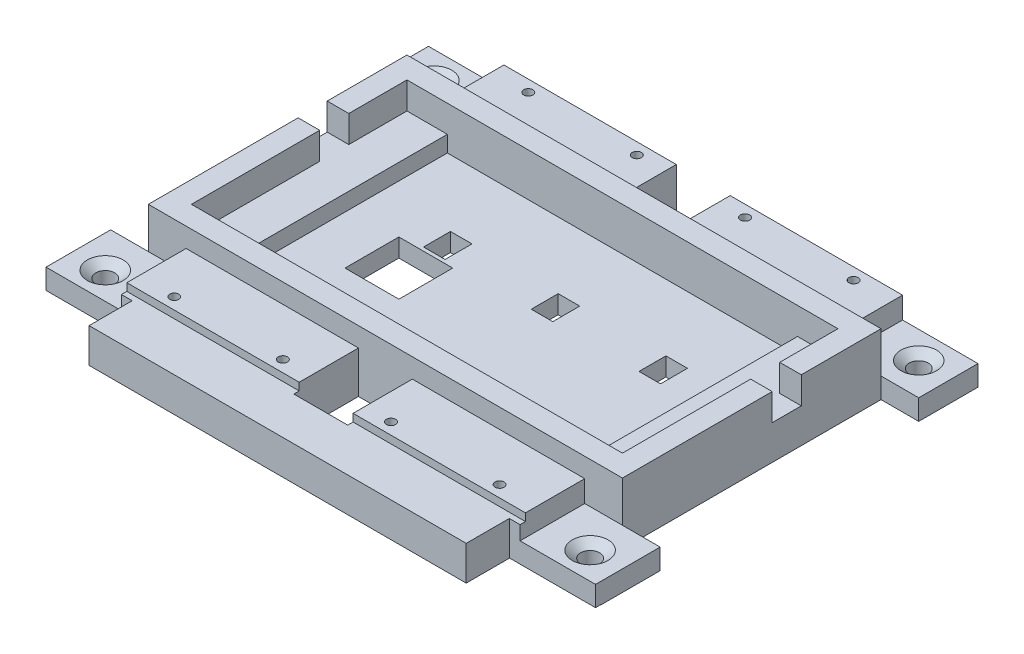
SolidWorks part; units mm, degrees
ref_plane "Front Plane" through (0, 0, 0) normal (0, 0, 1) x (1, 0, 0)
ref_plane "Top Plane" through (0, 0, 0) normal (0, 1, 0) x (1, 0, 0)
ref_plane "Right Plane" through (0, 0, 0) normal (1, 0, 0) x (0, 0, -1)
sketch "Sketch5" plane through (0, 5.08, 0) normal (0, 1, 0) x (1, 0, 0)
  line L0 (5.08, 5.08) -> (5.08, 248.92) construction
  line L1 (5.08, 105.41) -> (134.62, 105.41)
  line L2 (5.08, 105.41) -> (5.08, 16.51)
  line L3 (5.08, 16.51) -> (134.62, 16.51)
  line L4 (134.62, 105.41) -> (134.62, 16.51)
  line L6 (134.62, 248.92) -> (134.62, 5.08) construction
  point P8 (134.62, 60.96)
  dimension "D1" = 60.96
  dimension "D2" = 88.9
extrude "Button Support" add sketch "Sketch5" along normal blind 48.768
ref_plane "Plane1" through (0, 0, -60.96) normal (0, 0, 1) x (1, 0, 0)
sketch "Sketch6" plane through (0, 53.848, 0) normal (0, 1, 0) x (1, 0, 0)
  line L0 (0, 0) -> (139.7, 0) construction
  line L1 (19.05, 86.36) -> (120.65, 86.36)
  line L2 (19.05, 86.36) -> (19.05, 35.56)
  line L3 (19.05, 35.56) -> (120.65, 35.56)
  line L4 (120.65, 86.36) -> (120.65, 35.56)
  line L5 (125.73, 91.44) -> (13.97, 91.44)
  line L6 (125.73, 91.44) -> (125.73, 30.48)
  line L7 (125.73, 30.48) -> (13.97, 30.48)
  line L8 (13.97, 91.44) -> (13.97, 30.48)
  line L9 (134.62, 105.41) -> (5.08, 105.41) construction
  point P8 (69.85, 91.44)
  point P9 (69.85, 86.36)
  point P10 (120.65, 60.96)
  point P11 (125.73, 60.96)
  point P16 (69.85, 105.41)
  dimension "D1" = 50.8
  dimension "D2" = 60.96
  dimension "D3" = 101.6
  dimension "D4" = 5.08
  dimension "D5" = 5.08
extrude "Boss-Extrude4" add sketch "Sketch6" along normal blind 6.35
sketch "Sketch7" plane through (0, 53.848, 0) normal (0, 1, 0) x (1, 0, 0)
  line L1 (28.575, 35.56) -> (111.125, 35.56)
  line L2 (28.575, 35.56) -> (28.575, 86.36)
  line L3 (28.575, 86.36) -> (111.125, 86.36)
  line L4 (111.125, 35.56) -> (111.125, 86.36)
  line L5 (120.65, 86.36) -> (19.05, 86.36) construction
  line L7 (-5.4483, 60.96) -> (5.4483, 60.96) construction
  point P4 (28.575, 60.96)
  point P8 (69.85, 86.36)
  point P9 (69.85, 35.56)
  dimension "D1" = 82.55
  dimension "D2" = 50.8
other "AlignGroup1"
extrude "Force Sensor Cutout" cut sketch "Sketch7" against normal blind 3.81
sketch "Sketch4" plane through (0, 0, 0) normal (0, 0, 1) x (1, 0, 0)
  line L0 (0, 0) -> (139.7, 0) construction
  line L1 (5.08, 45.72) -> (134.62, 45.72)
  line L2 (5.08, 45.72) -> (5.08, 5.08)
  line L3 (5.08, 5.08) -> (134.62, 5.08)
  line L4 (134.62, 45.72) -> (134.62, 5.08)
  line L5 (0, 5.08) -> (0, 0) construction
  line L6 (139.7, 5.08) -> (139.7, 0) construction
  line L7 (0, 55.88) -> (139.7, 55.88) construction
  dimension "D1" = 5.08
  dimension "D2" = 5.08
  dimension "D3" = 5.08
  dimension "D4" = 10.16
extrude "Bottom Cut" cut sketch "Sketch4" against normal blind 139.7
sketch "Sketch25" plane through (0, 53.848, 0) normal (0, 1, 0) x (1, 0, 0)
  line L0 (134.62, 105.41) -> (5.08, 105.41) construction
  line L1 (13.97, 91.44) -> (125.73, 91.44)
  line L2 (13.97, 91.44) -> (13.97, 105.41)
  line L3 (13.97, 105.41) -> (125.73, 105.41)
  line L4 (125.73, 91.44) -> (125.73, 105.41)
  line L5 (5.08, 16.51) -> (134.62, 16.51) construction
  line L6 (125.73, 30.48) -> (13.97, 30.48)
  line L7 (125.73, 30.48) -> (125.73, 16.51)
  line L8 (125.73, 16.51) -> (13.97, 16.51)
  line L9 (13.97, 30.48) -> (13.97, 16.51)
  line L10 (125.73, 30.48) -> (125.73, 91.44) construction
  line L11 (13.97, 91.44) -> (13.97, 30.48) construction
extrude "NeoPixel Lift" add sketch "Sketch25" along normal blind 1.778
sketch "Sketch8" plane through (0, 50.038, 0) normal (0, 1, 0) x (1, 0, 0)
  line L0 (120.65, 86.36) -> (19.05, 86.36) construction
  line L1 (70.358, 64.353) -> (75.438, 64.353)
  line L2 (70.358, 64.353) -> (70.358, 70.703)
  line L3 (70.358, 70.703) -> (75.438, 70.703)
  line L4 (75.438, 64.353) -> (75.438, 70.703)
  line L5 (120.65, 35.56) -> (120.65, 86.36) construction
  line L6 (95.758, 64.353) -> (95.758, 70.703)
  line L7 (95.758, 64.353) -> (100.838, 64.353)
  line L8 (100.838, 64.353) -> (100.838, 70.703)
  line L9 (95.758, 70.703) -> (100.838, 70.703)
  line L10 (44.958, 64.353) -> (44.958, 70.703)
  line L11 (44.958, 64.353) -> (50.038, 64.353)
  line L12 (50.038, 64.353) -> (50.038, 70.703)
  line L13 (44.958, 70.703) -> (50.038, 70.703)
  dimension "D1" = 15.657
  dimension "D2" = 45.212
  dimension "D3" = 5.08
  dimension "D4" = 6.35
  dimension "D5" = 2
  dimension "D6" = 2
extrude "Haptic Wire Holes" cut sketch "Sketch8" against normal up to surface (4.318 mm away) up to face at (69.85, 45.72, -60.96)
sketch "Sketch9" plane through (0, 50.038, 0) normal (0, 1, 0) x (1, 0, 0)
  line L0 (120.65, 86.36) -> (19.05, 86.36) construction
  line L1 (52.705, 63.5) -> (40.005, 63.5)
  line L2 (52.705, 63.5) -> (52.705, 50.8)
  line L3 (52.705, 50.8) -> (40.005, 50.8)
  line L4 (40.005, 63.5) -> (40.005, 50.8)
  line L5 (28.575, 86.36) -> (28.575, 35.56) construction
  dimension "D1" = 12.7
  dimension "D2" = 12.7
  dimension "D3" = 22.86
  dimension "D4" = 11.43
extrude "Force Sensor Hole" cut sketch "Sketch9" against normal up to surface (4.318 mm away) up to face at (47.498, 45.72, -67.528)
sketch "Sketch10" plane through (0, 55.626, 0) normal (0, 1, 0) x (1, 0, 0)
  line L0 (5.08, 16.51) -> (13.97, 16.51) construction
  line L1 (134.62, 105.41) -> (134.62, 16.51) construction
  line L2 (-5.4483, 60.96) -> (5.4483, 60.96) construction
  circle A0 centre (108.0186, 19.2295) radius 1.0795
  circle A4 centre (82.4261, 19.2295) radius 1.0795
  circle A5 centre (56.9186, 19.2295) radius 1.0795
  circle A6 centre (31.3261, 19.2295) radius 1.0795
  circle A7 centre (31.3261, 102.6905) radius 1.0795
  circle A8 centre (56.9186, 102.6905) radius 1.0795
  circle A9 centre (82.4261, 102.6905) radius 1.0795
  circle A10 centre (108.0186, 102.6905) radius 1.0795
  dimension "D1" = 2.159
  dimension "D2" = 2.7195
  dimension "D3" = 26.6014
  dimension "D5" = 25.5925
  dimension "D6" = 25.5075
  dimension "D4" = 25.5925
extrude "NeoPixel Holes" cut sketch "Sketch10" against normal up to surface (9.906 mm away) up to face at (46.355, 45.72, -57.15)
sketch "Sketch18" plane through (0, 53.848, 0) normal (0, 1, 0) x (1, 0, 0)
  line L0 (134.62, 248.92) -> (134.62, 5.08) construction
  line L1 (125.73, 91.44) -> (134.62, 91.44)
  line L2 (125.73, 91.44) -> (125.73, 30.48)
  line L3 (125.73, 30.48) -> (134.62, 30.48)
  line L4 (134.62, 91.44) -> (134.62, 30.48)
  line L5 (5.08, 105.41) -> (5.08, 16.51) construction
  line L6 (13.97, 91.44) -> (5.08, 91.44)
  line L7 (13.97, 91.44) -> (13.97, 30.48)
  line L8 (13.97, 30.48) -> (5.08, 30.48)
  line L9 (5.08, 91.44) -> (5.08, 30.48)
  line L10 (13.97, 30.48) -> (125.73, 30.48) construction
extrude "Neopixel Wire Side Holes" cut sketch "Sketch18" against normal up to next
sketch "Sketch19" plane through (0, 55.626, 0) normal (0, 1, 0) x (1, 0, 0)
  line L0 (25.4, 105.41) -> (5.08, 105.41) construction
  line L1 (76.2, 105.41) -> (63.5, 105.41)
  line L2 (76.2, 105.41) -> (76.2, 91.44)
  line L3 (76.2, 91.44) -> (63.5, 91.44)
  line L4 (63.5, 105.41) -> (63.5, 91.44)
  line L5 (22.86, 105.41) -> (5.08, 105.41)
  line L6 (22.86, 105.41) -> (22.86, 91.44)
  line L7 (22.86, 91.44) -> (5.08, 91.44)
  line L8 (5.08, 105.41) -> (5.08, 91.44)
  line L9 (5.08, 105.41) -> (5.08, 91.44) construction
  line L10 (134.62, 105.41) -> (5.08, 105.41) construction
  line L11 (134.62, 105.41) -> (116.84, 105.41)
  line L12 (134.62, 105.41) -> (134.62, 91.44)
  line L13 (134.62, 91.44) -> (116.84, 91.44)
  line L14 (116.84, 105.41) -> (116.84, 91.44)
  line L15 (125.73, 91.44) -> (13.97, 91.44) construction
  point P19 (69.85, 105.41)
  point P20 (69.85, 105.41)
  dimension "D1" = 12.7
  dimension "D2" = 17.78
extrude "NeoPixel solder gap" cut sketch "Sketch19" against normal blind 5.08
mirror "Mirror1" about plane through (0, 0, -60.96) normal (0, 0, 1) of "NeoPixel solder gap"
sketch "Sketch20" plane through (0, 0, -16.51) normal (0, 0, 1) x (1, 0, 0)
  line L0 (134.62, 50.546) -> (134.62, 45.72) construction
  line L1 (5.08, 50.546) -> (134.62, 50.546)
  line L2 (5.08, 50.546) -> (5.08, 45.7868)
  line L3 (5.08, 45.7868) -> (134.62, 45.7868)
  line L4 (134.62, 50.546) -> (134.62, 45.7868)
  line L6 (116.84, 53.848) -> (76.2, 53.848)
  line L7 (116.84, 53.848) -> (116.84, 50.546)
  line L8 (116.84, 50.546) -> (76.2, 50.546)
  line L9 (76.2, 53.848) -> (76.2, 50.546)
  line L10 (22.86, 53.848) -> (63.5, 53.848)
  line L11 (22.86, 53.848) -> (22.86, 50.546)
  line L12 (22.86, 50.546) -> (63.5, 50.546)
  line L13 (63.5, 53.848) -> (63.5, 50.546)
extrude "Boss-Extrude6" add sketch "Sketch20" along normal blind 1.27
sketch "Sketch11" plane through (0, 0, -15.24) normal (0, 0, 1) x (1, 0, 0)
  line L0 (5.08, 45.7868) -> (5.08, 45.72) construction
  line L1 (25.4, 53.848) -> (114.3, 53.848)
  line L2 (25.4, 53.848) -> (25.4, 45.72)
  line L3 (25.4, 45.72) -> (114.3, 45.72)
  line L4 (114.3, 53.848) -> (114.3, 45.72)
  line L5 (134.62, 45.7868) -> (134.62, 45.72) construction
  line L6 (5.08, 53.848) -> (134.62, 53.848) construction
  line L7 (5.08, 45.72) -> (134.62, 45.72) construction
  dimension "D1" = 20.32
  dimension "D2" = 20.32
extrude "Boss-Extrude5" add sketch "Sketch11" along normal blind 10.16
hole_wizard "CSK for #8 Flat Head Machine Screw (100)1" positions "Sketch21" profile "Sketch22" countersink size "#8" standard "ANSI Inch" end condition through all
sketch "Sketch21" plane through (0, 50.546, 0) normal (0, 1, 0) x (1, 0, 0)
  line L0 (134.62, 91.44) -> (134.62, 105.41) construction
  line L1 (134.62, 105.41) -> (116.84, 105.41) construction
  line L2 (22.86, 15.24) -> (5.08, 15.24) construction
  line L3 (5.08, 15.24) -> (5.08, 30.48) construction
  point P0 (12.7, 99.06)
  point P2 (127, 99.06)
  point P4 (127, 21.59)
  point P6 (12.7, 21.59)
  dimension "D1" = 7.62
  dimension "D2" = 6.35
  dimension "D3" = 6.35
  dimension "D4" = 7.62
sketch "Sketch22" plane through (12.7, 50.546, -99.06) normal (1, 0, 0) x (0, 0, 1)
  line L0 (0, 0) -> (0, 4.826)
  line L1 (0, 4.826) -> (2.2479, 4.826)
  line L2 (2.2479, 4.826) -> (2.2479, 1.6518)
  line L3 (2.2479, 1.6518) -> (4.2164, 0)
  line L5 (4.2164, 0) -> (0, 0)
  line L6 (-2.2479, 1.6518) -> (-4.2164, 0) construction
  line L11 (0, -6.35) -> (0, 107.95) construction
  dimension "Thru Hole Dia." = 4.4958
  dimension "Thru Hole Depth" = 4.826
  dimension "Near C'Sink Dia." = 8.4328
  dimension "Near C'Sink Angle" = 100
sketch "Sketch23" plane through (0, 50.546, 0) normal (0, 1, 0) x (1, 0, 0)
  line L1 (63.5, 105.41) -> (76.2, 105.41)
  line L2 (63.5, 105.41) -> (63.5, 91.44)
  line L3 (63.5, 91.44) -> (76.2, 91.44)
  line L4 (76.2, 105.41) -> (76.2, 91.44)
  line L5 (63.5, 30.48) -> (76.2, 30.48)
  line L6 (63.5, 30.48) -> (63.5, 15.24)
  line L7 (63.5, 15.24) -> (76.2, 15.24)
  line L8 (76.2, 30.48) -> (76.2, 15.24)
extrude "Cut-Extrude1" cut sketch "Sketch23" against normal through all
sketch "Sketch24" plane through (125.73, 0, 0) normal (1, 0, 0) x (0, 0, -1)
  line L0 (30.48, 60.198) -> (91.44, 60.198) construction
  line L1 (72.644, 60.198) -> (65.786, 60.198)
  line L2 (72.644, 60.198) -> (72.644, 53.848)
  line L3 (72.644, 53.848) -> (65.786, 53.848)
  line L4 (65.786, 60.198) -> (65.786, 53.848)
  dimension "D1" = 13.716
  dimension "D2" = 6.858
  dimension "D3" = 6.35
extrude "Cut-Extrude2" cut sketch "Sketch24" against normal through all
equation "\"Arrow Height\"= 1.5in"
equation "\"Button Height\"= 2in"
equation "\"Button Width\"= 4in"
equation "\"Haptic Diameter\"= 10mm"
equation "\"Haptic Thickness\"= 2.7mm"
equation "\"Arrow Spacing\"= 1in"
equation "\"Arrow Width\"= 1in"
equation "\"Haptic Wire Angle\"= 63.43"
equation "\"Haptic Wire Width\"= .2in"
equation "\"Haptic Wire Height\"= .25in"
equation "\"Mounting Bolt Hole Diameter\"= .14in"
equation "\"D3@Sketch8\"=\"Haptic Wire Width\""
equation "\"D4@Sketch8\"=\"Haptic Wire Height\""
